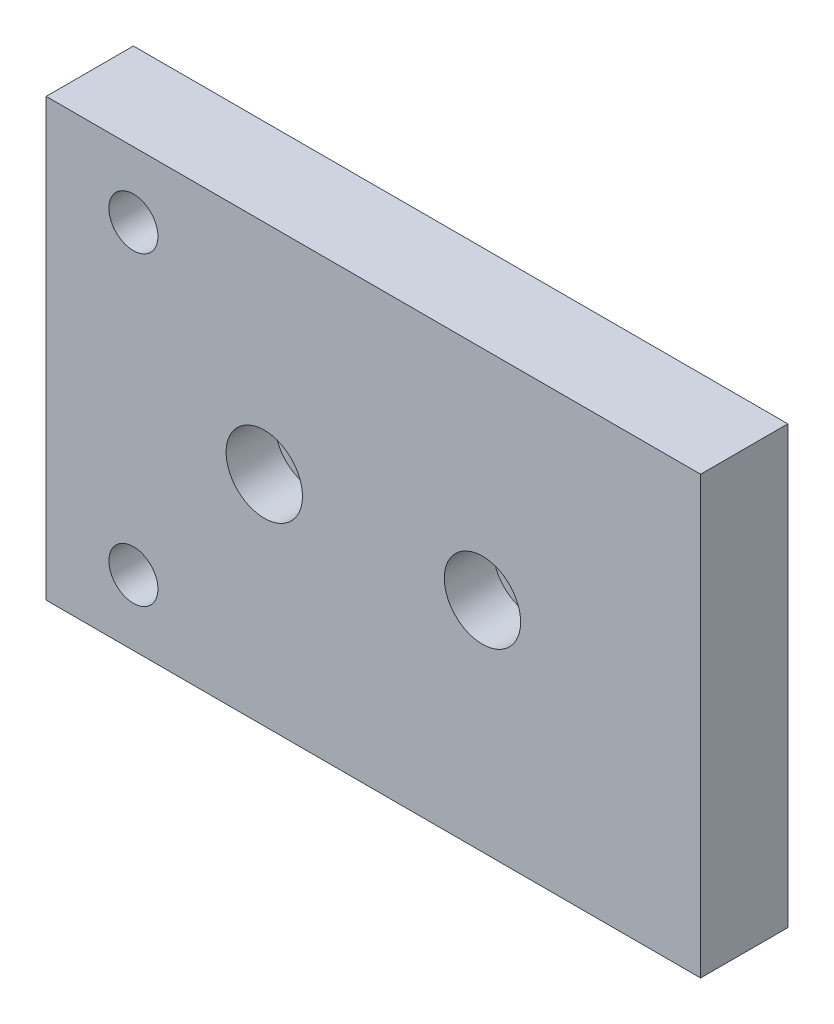
SolidWorks part; units mm, degrees
material "6061-T6 Al"
ref_plane "Front Plane" through (0, 0, 0) normal (0, 0, 1) x (1, 0, 0)
ref_plane "Top Plane" through (0, 0, 0) normal (0, 1, 0) x (1, 0, 0)
ref_plane "Right Plane" through (0, 0, 0) normal (1, 0, 0) x (0, 0, -1)
sketch "Sketch1" plane through (0, 0, 0) normal (0, 0, 1) x (1, 0, 0)
  line L1 (0, 0) -> (95.25, 0)
  line L2 (0, 0) -> (0, 63.5)
  line L3 (0, 63.5) -> (95.25, 63.5)
  line L4 (95.25, 0) -> (95.25, 63.5)
  dimension "D1" = 63.5
  dimension "D2" = 95.25
extrude "Boss-Extrude1" add sketch "Sketch1" along normal blind 12.7
hole_wizard "CBORE for 1/4 Socket Head Cap Screw1" positions "Sketch4" profile "Sketch3" counterbore size "1/4" standard "Ansi Inch" end condition through all
sketch "Sketch4" plane through (0, 0, 0) normal (0, 0, -1) x (-1, 0, 0)
  line L0 (-12.7, 9.525) -> (-12.7, 53.975) construction
  line L1 (0, 63.5) -> (0, 0) construction
  line L4 (0, 31.75) -> (-12.7, 31.75) construction
  line L5 (0, 63.5) -> (0, 0) construction
  point P0 (-12.7, 53.975)
  point P1 (-12.7, 9.525)
  dimension "D1" = 12.7
  dimension "D2" = 44.45
sketch "Sketch3" plane through (12.7, 53.975, 0) normal (1, 0, 0) x (0, 1, 0)
  line L0 (0, 0) -> (0, 12.7)
  line L1 (0, 12.7) -> (3.5712, 12.7)
  line L3 (3.5712, 12.7) -> (3.5712, 6.35)
  line L4 (3.5712, 6.35) -> (5.5562, 6.35)
  line L5 (5.5562, 6.35) -> (5.5562, 0)
  line L7 (5.5562, 0) -> (0, 0)
  line L11 (0, -6.35) -> (0, 107.95) construction
  dimension "Thru Hole Dia." = 7.1425
  dimension "Thru Hole Depth" = 12.7
  dimension "C'Bore Dia." = 11.1125
  dimension "C'Bore Depth" = 6.35
hole_wizard "CBORE for 1/4 Socket Head Cap Screw2" positions "Sketch8" profile "Sketch7" counterbore size "1/4" standard "Ansi Inch" end condition through all
sketch "Sketch8" plane through (0, 0, 12.7) normal (0, 0, 1) x (1, 0, 0)
  line L0 (31.75, 31.75) -> (63.5, 31.75) construction
  line L1 (0, 31.75) -> (31.75, 31.75) construction
  line L2 (0, 63.5) -> (0, 0) construction
  line L3 (47.625, 0) -> (47.625, 31.75) construction
  line L4 (0, 0) -> (95.25, 0) construction
  point P0 (31.75, 31.75)
  point P1 (63.5, 31.75)
  dimension "D2" = 31.75
sketch "Sketch7" plane through (31.75, 31.75, 12.7) normal (1, 0, 0) x (0, -1, 0)
  line L0 (0, 0) -> (0, 12.7)
  line L1 (0, 12.7) -> (3.5712, 12.7)
  line L3 (3.5712, 12.7) -> (3.5712, 7.112)
  line L4 (3.5712, 7.112) -> (5.5562, 7.112)
  line L5 (5.5562, 7.112) -> (5.5562, 0)
  line L7 (5.5562, 0) -> (0, 0)
  line L11 (0, -6.35) -> (0, 107.95) construction
  dimension "Thru Hole Dia." = 7.1425
  dimension "Thru Hole Depth" = 12.7
  dimension "C'Bore Dia." = 11.1125
  dimension "C'Bore Depth" = 7.112
